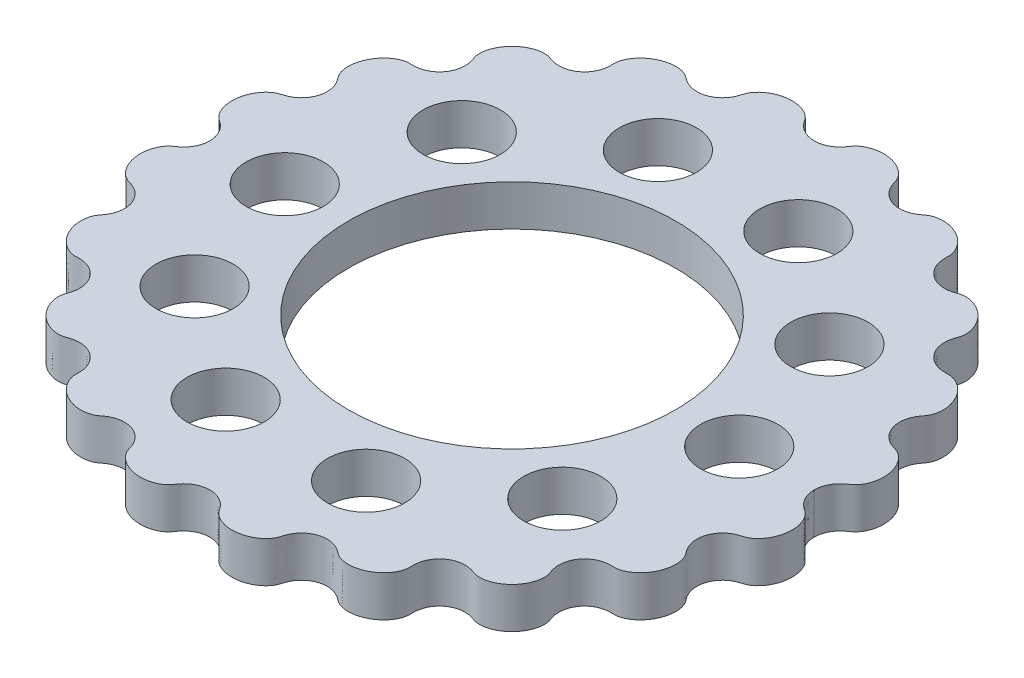
SolidWorks part; units mm, degrees
ref_plane "Front Plane" through (0, 0, 0) normal (0, 0, 1) x (1, 0, 0)
ref_plane "Top Plane" through (0, 0, 0) normal (0, 1, 0) x (1, 0, 0)
ref_plane "Right Plane" through (0, 0, 0) normal (1, 0, 0) x (0, 0, -1)
sketch "Sketch1" plane through (0, 0, 0) normal (0, 1, 0) x (1, 0, 0)
  line L0 (-115.1642, 0) -> (115.1642, 0) construction
  line L1 (0, 0) -> (50, 0)
  circle A0 centre (0, 0) radius 36
  circle A1 centre (50, 0) radius 8.5
  circle A2 centre (40.4508, -29.3893) radius 8.5
  circle A3 centre (15.4508, -47.5528) radius 8.5
  circle A4 centre (-15.4508, -47.5528) radius 8.5
  circle A5 centre (-40.4508, -29.3893) radius 8.5
  circle A6 centre (-50, 0) radius 8.5
  circle A7 centre (-40.4508, 29.3893) radius 8.5
  circle A8 centre (-15.4508, 47.5528) radius 8.5
  circle A9 centre (15.4508, 47.5528) radius 8.5
  circle A10 centre (40.4508, 29.3893) radius 8.5
  spline S0 degree 4 poles (65.4605, 29.5127) (65.4655, 29.1686) (65.4411, 28.6953) (65.3529, 28.0968) (65.1422, 27.3959) (64.9669, 26.9794) (64.7793, 26.6408) (64.5721, 26.3406) (64.3602, 26.0705) (64.1267, 25.7629) (63.886, 25.4071) (63.6576, 25.018) (63.4493, 24.5932) (63.2212, 24.0118) (63.0252, 23.2599) (62.9311, 22.3562) (63.0135, 21.3212) (63.2874, 20.3043) (63.7526, 19.3426) (64.4013, 18.4733) (65.1379, 17.8054) (65.8842, 17.3263) (66.5245, 17.0291) (66.9742, 16.8668) (67.3149, 16.7623) (67.5855, 16.6832) (67.8556, 16.6018) (68.139, 16.4927) (68.4292, 16.347) (68.7442, 16.1592) (69.1239, 15.8899) (69.5685, 15.5009) (70.0111, 15.0131) (70.4008, 14.4816) (70.6777, 14.0268) (70.8691, 13.6636) (70.9988, 13.3869) (71.0782, 13.2046) (71.1589, 13.0042) (71.23, 12.8148) (71.2726, 12.6939) (71.3209, 12.5457) (71.3774, 12.3645) (71.4665, 12.0546) (71.5573, 11.6609) (71.6461, 11.1378) (71.6973, 10.5855) (71.7141, 10.0755) (71.6934, 9.4422) (71.604, 8.684) (71.4252, 7.9197) (71.1461, 7.1625) (70.8392, 6.5565) (70.5425, 6.0894) (70.2317, 5.6994) (69.9193, 5.3829) (69.5974, 5.1276) (69.2839, 4.9185) (68.9179, 4.6631) (68.5115, 4.3444) (68.0178, 3.8822) (67.479, 3.228) (67.0049, 2.4212) (66.6487, 1.4477) (66.4722, 0.3979) (66.4959, -0.6726) (66.728, -1.7332) (67.1223, -2.6449) (67.6013, -3.3859) (68.0735, -3.9308) (68.4846, -4.3184) (68.8764, -4.6317) (69.2337, -4.8858) (69.5643, -5.1036) (69.8432, -5.3215) (70.1179, -5.5817) (70.4008, -5.9017) (70.7023, -6.3238) (71.0546, -6.9527) (71.3757, -7.7472) (71.6154, -8.6857) (71.7312, -9.759) (71.7014, -10.8232) (71.5361, -11.8601) (71.2442, -12.8535) (70.8335, -13.7883) (70.3588, -14.5657) (69.8607, -15.1916) (69.3853, -15.6662) (68.9647, -16.0122) (68.5481, -16.287) (68.1887, -16.4718) (67.8853, -16.5895) (67.6027, -16.679) (67.3177, -16.7605) (66.9147, -16.8851) (66.4027, -17.0799) (65.771, -17.3914) (65.047, -17.8802) (64.3539, -18.5333) (63.7378, -19.3727) (63.275, -20.3353) (63.0008, -21.3699) (62.9289, -22.4535) (63.0528, -23.4279) (63.2978, -24.2511) (63.587, -24.8932) (63.8609, -25.3718) (64.1452, -25.79) (64.4255, -26.1537) (64.7197, -26.5327) (64.9654, -26.9687) (65.1645, -27.4552) (65.3153, -27.9862) (65.4369, -28.6607) (65.4867, -29.4797) (65.4211, -30.426) (65.1959, -31.4778) (64.8335, -32.4836) (64.3459, -33.4278) (63.7436, -34.2955) (63.0364, -35.0719) (62.3194, -35.6676) (61.6326, -36.1029) (61.0186, -36.3975) (60.5014, -36.5851) (60.0027, -36.7056) (59.5828, -36.7546) (59.2387, -36.7552) (58.9195, -36.7455) (58.6002, -36.738) (58.1866, -36.7449) (57.6806, -36.7888) (57.0258, -36.9034) (56.2311, -37.1486) (55.3802, -37.5682) (54.5248, -38.2129) (53.7989, -39.0162) (53.2457, -39.9314) (52.8764, -40.9322) (52.7129, -41.9038) (52.7111, -42.801) (52.8153, -43.5274) (52.9414, -44.0332) (53.0556, -44.396) (53.1493, -44.6684) (53.2479, -44.939) (53.365, -45.2914) (53.4522, -45.7377) (53.492, -46.2577) (53.4686, -46.8459) (53.3634, -47.5564) (53.1367, -48.3745) (52.7684, -49.2465) (52.2349, -50.1437) (51.5838, -50.9705) (50.825, -51.7126) (49.9786, -52.3468) (49.0582, -52.8607) (48.2008, -53.1936) (47.4397, -53.384) (46.7836, -53.4712) (46.2434, -53.4905) (45.7356, -53.453) (45.3175, -53.3699) (44.9917, -53.2655) (44.6996, -53.161) (44.407, -53.0576) (44.0063, -52.933) (43.491, -52.8115) (42.8001, -52.7145) (41.9272, -52.71) (40.953, -52.8675) (39.9202, -53.2489) (38.9741, -53.8277) (38.1691, -54.5703) (37.5299, -55.4429) (37.1019, -56.344) (36.8793, -57.1248) (36.7803, -57.7595) (36.7454, -58.2289) (36.7381, -58.5957) (36.7456, -58.9543) (36.7588, -59.3048) (36.7453, -59.7001) (36.6779, -60.1352) (36.5493, -60.6146) (36.3491, -61.1297) (36.0405, -61.7408) (35.5897, -62.4233) (34.9769, -63.1346) (34.1812, -63.8335) (33.2956, -64.4242) (32.3354, -64.8968) (31.316, -65.2408) (30.2533, -65.4441) (29.3028, -65.4867) (28.4861, -65.415) (27.8172, -65.2736) (27.3586, -65.1269) (26.9828, -64.9645) (26.6415, -64.7795) (26.3825, -64.6044) (26.1435, -64.417) (25.8617, -64.202) (25.5735, -63.9954) (25.2136, -63.7661) (24.7736, -63.5314) (24.1733, -63.2738) (23.3906, -63.046) (22.4364, -62.9272) (21.3345, -63.0057) (20.2693, -63.297) (19.3028, -63.7777) (18.4651, -64.4155) (17.8212, -65.1237) (17.3489, -65.8446) (17.0492, -66.4737) (16.8796, -66.9362) (16.7731, -67.2787) (16.697, -67.538) (16.6206, -67.7971) (16.4999, -68.13) (16.3026, -68.5209) (16.0236, -68.9517) (15.6499, -69.4069) (15.1392, -69.9099) (14.4692, -70.4259) (13.6607, -70.8988) (12.7127, -71.2944) (11.702, -71.5708) (10.6433, -71.7174) (9.5744, -71.7223) (8.5152, -71.5812) (7.6197, -71.3301) (6.8918, -71.0218) (6.3681, -70.7238) (6.0257, -70.4887) (5.7564, -70.2722) (5.5526, -70.086) (5.3293, -69.8531) (5.1014, -69.5624) (4.8738, -69.215) (4.6046, -68.8398) (4.2946, -68.4584) (3.9347, -68.0813) (3.4174, -67.6285) (2.7042, -67.1529) (1.7921, -66.7433) (0.6851, -66.4941) (-0.4667, -66.4704) (-1.4606, -66.6552) (-2.2728, -66.9558) (-2.9107, -67.2974) (-3.3788, -67.6111) (-3.7983, -67.9554) (-4.1704, -68.3213) (-4.4603, -68.6577) (-4.6823, -68.9486) (-4.8581, -69.1976) (-4.9952, -69.3993) (-5.1396, -69.6076) (-5.3007, -69.8157) (-5.4839, -70.0179) (-5.6881, -70.2127) (-5.9591, -70.4393) (-6.3053, -70.6848) (-6.8327, -70.9933) (-7.5648, -71.3113) (-8.469, -71.5723) (-9.5418, -71.7212) (-10.6244, -71.7198) (-11.6959, -71.5725) (-12.7127, -71.2944) (-13.6607, -70.8988) (-14.4692, -70.4259) (-15.1392, -69.9099) (-15.6499, -69.4069) (-16.0236, -68.9517) (-16.3026, -68.5209) (-16.4999, -68.13) (-16.6206, -67.7971) (-16.697, -67.538) (-16.7731, -67.2787) (-16.8796, -66.9362) (-17.0492, -66.4737) (-17.3489, -65.8446) (-17.8212, -65.1237) (-18.4651, -64.4155) (-19.3028, -63.7777) (-20.2693, -63.297) (-21.3345, -63.0057) (-22.4364, -62.9272) (-23.3906, -63.046) (-24.1733, -63.2738) (-24.7736, -63.5314) (-25.2137, -63.7661) (-25.5735, -63.9954) (-25.8617, -64.202) (-26.0964, -64.3813) (-26.2831, -64.5262) (-26.4805, -64.6709) (-26.6936, -64.8076) (-26.9828, -64.9646) (-27.3587, -65.1269) (-27.8172, -65.2736) (-28.4861, -65.415) (-29.3028, -65.4868) (-30.2533, -65.4441) (-31.316, -65.2408) (-32.3354, -64.8968) (-33.2956, -64.4242) (-34.1812, -63.8335) (-34.9769, -63.1346) (-35.5897, -62.4233) (-36.0405, -61.7408) (-36.3491, -61.1297) (-36.5493, -60.6146) (-36.6779, -60.1352) (-36.7453, -59.7001) (-36.7588, -59.3048) (-36.7456, -58.9543) (-36.7381, -58.5957) (-36.7454, -58.2289) (-36.7803, -57.7595) (-36.8793, -57.1248) (-37.1019, -56.344) (-37.5299, -55.4429) (-38.1691, -54.5703) (-38.9741, -53.8277) (-39.9202, -53.2489) (-40.953, -52.8675) (-41.9272, -52.71) (-42.8001, -52.7145) (-43.491, -52.8115) (-44.0063, -52.933) (-44.407, -53.0576) (-44.6996, -53.161) (-44.9917, -53.2655) (-45.3175, -53.3699) (-45.7356, -53.453) (-46.2434, -53.4905) (-46.7836, -53.4712) (-47.4397, -53.384) (-48.2008, -53.1936) (-49.0582, -52.8607) (-49.9786, -52.3468) (-50.825, -51.7126) (-51.5838, -50.9705) (-52.2349, -50.1437) (-52.7684, -49.2465) (-53.1367, -48.3745) (-53.3634, -47.5564) (-53.4686, -46.8459) (-53.492, -46.2577) (-53.4522, -45.7377) (-53.365, -45.2914) (-53.2479, -44.939) (-53.1493, -44.6684) (-53.0556, -44.396) (-52.9697, -44.1229) (-52.8837, -43.8018) (-52.7883, -43.3387) (-52.7113, -42.7066) (-52.7129, -41.9038) (-52.8764, -40.9322) (-53.2457, -39.9314) (-53.7989, -39.0162) (-54.5248, -38.2129) (-55.3802, -37.5682) (-56.2311, -37.1486) (-57.0258, -36.9034) (-57.6806, -36.7888) (-58.1866, -36.7449) (-58.6002, -36.738) (-58.9195, -36.7455) (-59.2387, -36.7552) (-59.5828, -36.7546) (-60.0027, -36.7056) (-60.5014, -36.5851) (-61.0186, -36.3975) (-61.6326, -36.1029) (-62.3194, -35.6676) (-63.0364, -35.0719) (-63.7436, -34.2955) (-64.3459, -33.4278) (-64.8335, -32.4836) (-65.1959, -31.4778) (-65.4211, -30.426) (-65.4867, -29.4797) (-65.4369, -28.6607) (-65.3153, -27.9862) (-65.1645, -27.4552) (-64.9654, -26.9687) (-64.7197, -26.5327) (-64.4255, -26.1537) (-64.1452, -25.79) (-63.8609, -25.3718) (-63.587, -24.8932) (-63.2978, -24.2511) (-63.0528, -23.4279) (-62.9289, -22.4535) (-63.0008, -21.3699) (-63.275, -20.3353) (-63.7378, -19.3727) (-64.3539, -18.5333) (-65.047, -17.8802) (-65.771, -17.3914) (-66.4027, -17.0799) (-66.9147, -16.8851) (-67.3177, -16.7605) (-67.6027, -16.679) (-67.8853, -16.5895) (-68.1887, -16.4718) (-68.5481, -16.287) (-68.9647, -16.0122) (-69.3853, -15.6662) (-69.8607, -15.1916) (-70.3588, -14.5657) (-70.8335, -13.7883) (-71.2442, -12.8535) (-71.5361, -11.8601) (-71.7014, -10.8232) (-71.7312, -9.759) (-71.6154, -8.6857) (-71.3757, -7.7472) (-71.0546, -6.9527) (-70.7023, -6.3238) (-70.4008, -5.9017) (-70.1179, -5.5817) (-69.8432, -5.3215) (-69.5643, -5.1036) (-69.2337, -4.8858) (-68.8764, -4.6317) (-68.4846, -4.3184) (-68.0735, -3.9308) (-67.6013, -3.3859) (-67.1223, -2.6449) (-66.728, -1.7332) (-66.4959, -0.6726) (-66.4722, 0.3979) (-66.6487, 1.4477) (-67.0049, 2.4212) (-67.479, 3.228) (-68.0178, 3.8822) (-68.5115, 4.3445) (-68.9179, 4.6631) (-69.2839, 4.9185) (-69.5974, 5.1275) (-69.9193, 5.3829) (-70.2317, 5.6994) (-70.5425, 6.0895) (-70.8393, 6.5564) (-71.1461, 7.1627) (-71.4254, 7.9193) (-71.6038, 8.6846) (-71.6937, 9.4414) (-71.7137, 10.0768) (-71.6982, 10.5829) (-71.6528, 11.0541) (-71.5898, 11.476) (-71.5079, 11.8717) (-71.4425, 12.139) (-71.3774, 12.3645) (-71.3208, 12.546) (-71.2727, 12.6938) (-71.23, 12.8149) (-71.1589, 13.0042) (-71.0782, 13.2046) (-70.9988, 13.3869) (-70.8691, 13.6636) (-70.6777, 14.0268) (-70.4008, 14.4816) (-70.0111, 15.0131) (-69.5685, 15.5009) (-69.1239, 15.8899) (-68.7442, 16.1592) (-68.4292, 16.347) (-68.139, 16.4927) (-67.8556, 16.6018) (-67.5855, 16.6832) (-67.3149, 16.7623) (-66.9742, 16.8668) (-66.5245, 17.0291) (-65.8842, 17.3263) (-65.1379, 17.8054) (-64.4013, 18.4733) (-63.7491, 19.3473) (-63.28, 20.3205) (-63.0059, 21.3554) (-62.9309, 22.4063) (-63.0352, 23.3171) (-63.2396, 24.0678) (-63.4711, 24.642) (-63.6812, 25.0611) (-63.9101, 25.4449) (-64.1204, 25.7515) (-64.3116, 26.0062) (-64.4807, 26.2243) (-64.6214, 26.4108) (-64.7943, 26.6657) (-64.9775, 27.0024) (-65.1491, 27.4157) (-65.3551, 28.1105) (-65.4416, 28.7032) (-65.4654, 29.172) (-65.4605, 29.5127) knots 0 0 0 0 0 0.004123 0.005669 0.007215 0.008756 0.009527 0.010298 0.011583 0.012869 0.014155 0.015441 0.016987 0.018533 0.02163 0.024723 0.027815 0.030907 0.034179 0.03745 0.040732 0.042749 0.044767 0.045893 0.046456 0.04702 0.048146 0.049273 0.050089 0.050906 0.052538 0.054845 0.057151 0.058784 0.060416 0.061233 0.062049 0.062457 0.062865 0.063682 0.064216 0.064483 0.06475 0.065818 0.067955 0.069475 0.070996 0.072517 0.074037 0.077079 0.08012 0.0819 0.08368 0.085209 0.086738 0.087867 0.088995 0.090124 0.091252 0.093215 0.095179 0.098214 0.101374 0.104369 0.107533 0.1109 0.114125 0.117298 0.119365 0.121433 0.122746 0.124059 0.125372 0.126686 0.12749 0.128294 0.129902 0.131797 0.133692 0.136915 0.140139 0.143363 0.146587 0.149637 0.152687 0.155738 0.158788 0.160518 0.162248 0.163776 0.165304 0.166488 0.16708 0.167672 0.168855 0.170039 0.172134 0.174229 0.177278 0.18047 0.183483 0.186637 0.190007 0.193215 0.196415 0.198338 0.200262 0.201638 0.203015 0.204391 0.205768 0.207378 0.208989 0.210679 0.212369 0.215581 0.218794 0.222006 0.225218 0.228355 0.231492 0.234629 0.237765 0.239488 0.24121 0.242778 0.244347 0.245622 0.24626 0.246898 0.248174 0.24945 0.251214 0.252979 0.256128 0.259382 0.262517 0.265738 0.269027 0.272117 0.275225 0.277481 0.279736 0.280887 0.281463 0.282038 0.283189 0.28434 0.285906 0.287472 0.289426 0.29138 0.294497 0.297615 0.300733 0.30385 0.307074 0.310298 0.313371 0.316443 0.31806 0.319676 0.321293 0.322909 0.324149 0.324768 0.325388 0.326627 0.327867 0.329796 0.331725 0.334972 0.338289 0.341548 0.344836 0.34818 0.35133 0.354431 0.356724 0.35787 0.359017 0.360068 0.361118 0.362169 0.36322 0.3648 0.366381 0.368106 0.36983 0.372993 0.376156 0.379319 0.382483 0.385713 0.388944 0.392175 0.395406 0.397073 0.39874 0.400356 0.401164 0.401972 0.403388 0.404096 0.404804 0.40622 0.407635 0.409205 0.410774 0.414037 0.417372 0.420655 0.423928 0.427187 0.430227 0.4332 0.43534 0.437479 0.438558 0.439098 0.439638 0.440717 0.441796 0.443334 0.444872 0.446856 0.44884 0.451909 0.454977 0.458046 0.461115 0.464432 0.467749 0.470814 0.47388 0.475539 0.477198 0.478024 0.478851 0.479677 0.480504 0.481887 0.48327 0.484653 0.486036 0.487772 0.489508 0.492878 0.49627 0.499675 0.503014 0.506592 0.508301 0.51001 0.511672 0.513334 0.514795 0.516256 0.516987 0.517718 0.518448 0.519179 0.520024 0.520869 0.521714 0.522559 0.524254 0.525949 0.529024 0.532099 0.535492 0.538885 0.541954 0.545023 0.548091 0.55116 0.553144 0.555128 0.556666 0.558204 0.559283 0.560362 0.560902 0.561442 0.562521 0.56466 0.5668 0.569773 0.572812 0.576072 0.579345 0.582628 0.585963 0.589226 0.590795 0.592365 0.59378 0.595196 0.595904 0.596612 0.59732 0.598028 0.598836 0.599644 0.60126 0.602927 0.604594 0.607825 0.611056 0.614287 0.617517 0.620681 0.623844 0.627007 0.63017 0.631894 0.633619 0.635199 0.63678 0.637831 0.638882 0.639932 0.640983 0.64213 0.643276 0.645569 0.64867 0.65182 0.655164 0.658452 0.661711 0.665028 0.668275 0.670204 0.672133 0.673372 0.674612 0.675232 0.675851 0.677091 0.678707 0.680324 0.68194 0.683557 0.686629 0.689702 0.692926 0.69615 0.699267 0.702385 0.705503 0.70862 0.710574 0.712528 0.714094 0.71566 0.716811 0.717962 0.718537 0.719113 0.720264 0.721391 0.722519 0.724775 0.727883 0.730973 0.734262 0.737483 0.740618 0.743872 0.747021 0.748786 0.75055 0.751826 0.753102 0.75374 0.754378 0.755653 0.757222 0.75879 0.760512 0.762234 0.765371 0.768508 0.771645 0.774782 0.777994 0.781206 0.784419 0.787631 0.789321 0.791011 0.792622 0.794232 0.795609 0.796985 0.798362 0.799738 0.801662 0.803585 0.806785 0.809993 0.813363 0.816517 0.81953 0.822722 0.825771 0.827866 0.829961 0.831145 0.832328 0.83292 0.833512 0.834696 0.836224 0.837752 0.839482 0.841212 0.844262 0.847313 0.850363 0.853413 0.856637 0.859861 0.863084 0.866308 0.868203 0.870098 0.871706 0.87251 0.873314 0.874628 0.875941 0.877254 0.878567 0.880635 0.882702 0.885875 0.8891 0.892467 0.895631 0.898626 0.901786 0.904821 0.906785 0.908748 0.909876 0.911005 0.912133 0.913262 0.914791 0.91632 0.9181 0.91988 0.922921 0.925963 0.927483 0.929004 0.930525 0.932045 0.933114 0.934182 0.93525 0.935517 0.935784 0.936318 0.937135 0.937543 0.937951 0.938767 0.939584 0.941216 0.942849 0.945155 0.947462 0.949094 0.949911 0.950727 0.951854 0.95298 0.953544 0.954107 0.955233 0.957251 0.959268 0.96255 0.965821 0.969093 0.972255 0.975418 0.978575 0.981646 0.98318 0.984714 0.985986 0.987258 0.98853 0.989166 0.989802 0.990566 0.991329 0.992855 0.994386 0.995917 1 1 1 1 1 construction
  spline S1 degree 4 poles (66.5, 0) (66.5, -0.3064) (66.5419, -0.882) (66.7179, -1.7097) (67.1223, -2.6449) (67.6013, -3.3859) (68.0735, -3.9308) (68.4846, -4.3184) (68.8764, -4.6317) (69.2337, -4.8858) (69.5643, -5.1036) (69.8432, -5.3215) (70.1179, -5.5817) (70.4008, -5.9017) (70.7023, -6.3238) (71.0546, -6.9527) (71.3757, -7.7472) (71.6154, -8.6857) (71.7312, -9.759) (71.7014, -10.8232) (71.5361, -11.8601) (71.2442, -12.8535) (70.8335, -13.7883) (70.3588, -14.5657) (69.8607, -15.1916) (69.3853, -15.6662) (68.9647, -16.0122) (68.5481, -16.287) (68.1887, -16.4718) (67.8853, -16.5895) (67.6027, -16.679) (67.3177, -16.7605) (66.9147, -16.8851) (66.4027, -17.0799) (65.771, -17.3914) (65.047, -17.8802) (64.3539, -18.5333) (63.7378, -19.3727) (63.275, -20.3353) (63.0008, -21.3699) (62.9289, -22.4535) (63.0528, -23.4279) (63.2978, -24.2511) (63.587, -24.8932) (63.8609, -25.3718) (64.1452, -25.79) (64.4255, -26.1537) (64.7197, -26.5327) (64.9654, -26.9687) (65.1645, -27.4552) (65.3153, -27.9862) (65.4369, -28.6607) (65.4867, -29.4797) (65.4211, -30.426) (65.1959, -31.4778) (64.8335, -32.4836) (64.3459, -33.4278) (63.7436, -34.2955) (63.0364, -35.0719) (62.3194, -35.6676) (61.6326, -36.1029) (61.0186, -36.3975) (60.5014, -36.5851) (60.0027, -36.7056) (59.5828, -36.7546) (59.2387, -36.7552) (58.9195, -36.7455) (58.6002, -36.738) (58.1866, -36.7449) (57.6806, -36.7888) (57.0258, -36.9034) (56.2311, -37.1486) (55.3802, -37.5682) (54.5248, -38.2129) (53.7989, -39.0162) (53.2457, -39.9314) (52.8764, -40.9322) (52.7129, -41.9038) (52.7111, -42.801) (52.8153, -43.5274) (52.9414, -44.0332) (53.0556, -44.396) (53.1493, -44.6684) (53.2479, -44.939) (53.365, -45.2914) (53.4522, -45.7377) (53.492, -46.2577) (53.4686, -46.8459) (53.3634, -47.5564) (53.1367, -48.3745) (52.7684, -49.2465) (52.2349, -50.1437) (51.5838, -50.9705) (50.825, -51.7126) (49.9786, -52.3468) (49.0582, -52.8607) (48.2008, -53.1936) (47.4397, -53.384) (46.7836, -53.4712) (46.2434, -53.4905) (45.7356, -53.453) (45.3175, -53.3699) (44.9917, -53.2655) (44.6996, -53.161) (44.407, -53.0576) (44.0063, -52.933) (43.491, -52.8115) (42.8001, -52.7145) (41.9272, -52.71) (40.953, -52.8675) (39.9202, -53.2489) (38.9741, -53.8277) (38.1691, -54.5703) (37.5299, -55.4429) (37.1019, -56.344) (36.8793, -57.1248) (36.7803, -57.7595) (36.7454, -58.2289) (36.7381, -58.5957) (36.7456, -58.9543) (36.7588, -59.3048) (36.7453, -59.7001) (36.6779, -60.1352) (36.5493, -60.6146) (36.3491, -61.1297) (36.0405, -61.7408) (35.5897, -62.4233) (34.9769, -63.1346) (34.1812, -63.8335) (33.2956, -64.4242) (32.3354, -64.8968) (31.316, -65.2408) (30.2533, -65.4441) (29.3028, -65.4867) (28.4861, -65.415) (27.8172, -65.2736) (27.3586, -65.1269) (26.9828, -64.9645) (26.6415, -64.7795) (26.3825, -64.6044) (26.1435, -64.417) (25.8617, -64.202) (25.5735, -63.9954) (25.2136, -63.7661) (24.7736, -63.5314) (24.1733, -63.2738) (23.3906, -63.046) (22.4364, -62.9272) (21.3345, -63.0057) (20.2693, -63.297) (19.3028, -63.7777) (18.4651, -64.4155) (17.8212, -65.1237) (17.3489, -65.8446) (17.0492, -66.4737) (16.8796, -66.9362) (16.7731, -67.2787) (16.697, -67.538) (16.6206, -67.7971) (16.4999, -68.13) (16.3026, -68.5209) (16.0236, -68.9517) (15.6499, -69.4069) (15.1392, -69.9099) (14.4692, -70.4259) (13.6607, -70.8988) (12.7127, -71.2944) (11.702, -71.5708) (10.6433, -71.7174) (9.5744, -71.7223) (8.5152, -71.5812) (7.6197, -71.3301) (6.8918, -71.0218) (6.3681, -70.7238) (6.0257, -70.4887) (5.7564, -70.2722) (5.5526, -70.086) (5.3293, -69.8531) (5.1014, -69.5624) (4.8738, -69.215) (4.6046, -68.8398) (4.2946, -68.4584) (3.9347, -68.0813) (3.4174, -67.6285) (2.7042, -67.1529) (1.7921, -66.7433) (0.6851, -66.4941) (-0.4667, -66.4704) (-1.4606, -66.6552) (-2.2728, -66.9558) (-2.9107, -67.2974) (-3.3788, -67.6111) (-3.7983, -67.9554) (-4.1704, -68.3213) (-4.4603, -68.6577) (-4.6823, -68.9486) (-4.8581, -69.1976) (-4.9952, -69.3993) (-5.1396, -69.6076) (-5.3007, -69.8157) (-5.4839, -70.0179) (-5.6881, -70.2127) (-5.9591, -70.4393) (-6.3053, -70.6848) (-6.8327, -70.9933) (-7.5648, -71.3113) (-8.469, -71.5723) (-9.5418, -71.7212) (-10.6244, -71.7198) (-11.6959, -71.5725) (-12.7127, -71.2944) (-13.6607, -70.8988) (-14.4692, -70.4259) (-15.1392, -69.9099) (-15.6499, -69.4069) (-16.0236, -68.9517) (-16.3026, -68.5209) (-16.4999, -68.13) (-16.6206, -67.7971) (-16.697, -67.538) (-16.7731, -67.2787) (-16.8796, -66.9362) (-17.0492, -66.4737) (-17.3489, -65.8446) (-17.8212, -65.1237) (-18.4651, -64.4155) (-19.3028, -63.7777) (-20.2693, -63.297) (-21.3345, -63.0057) (-22.4364, -62.9272) (-23.3906, -63.046) (-24.1733, -63.2738) (-24.7736, -63.5314) (-25.2137, -63.7661) (-25.5735, -63.9954) (-25.8617, -64.202) (-26.0964, -64.3813) (-26.2831, -64.5262) (-26.4805, -64.6709) (-26.6936, -64.8076) (-26.9828, -64.9646) (-27.3587, -65.1269) (-27.8172, -65.2736) (-28.4861, -65.415) (-29.3028, -65.4868) (-30.2533, -65.4441) (-31.316, -65.2408) (-32.3354, -64.8968) (-33.2956, -64.4242) (-34.1812, -63.8335) (-34.9769, -63.1346) (-35.5897, -62.4233) (-36.0405, -61.7408) (-36.3491, -61.1297) (-36.5493, -60.6146) (-36.6779, -60.1352) (-36.7453, -59.7001) (-36.7588, -59.3048) (-36.7456, -58.9543) (-36.7381, -58.5957) (-36.7454, -58.2289) (-36.7803, -57.7595) (-36.8793, -57.1248) (-37.1019, -56.344) (-37.5299, -55.4429) (-38.1691, -54.5703) (-38.9741, -53.8277) (-39.9202, -53.2489) (-40.953, -52.8675) (-41.9272, -52.71) (-42.8001, -52.7145) (-43.491, -52.8115) (-44.0063, -52.933) (-44.407, -53.0576) (-44.6996, -53.161) (-44.9917, -53.2655) (-45.3175, -53.3699) (-45.7356, -53.453) (-46.2434, -53.4905) (-46.7836, -53.4712) (-47.4397, -53.384) (-48.2008, -53.1936) (-49.0582, -52.8607) (-49.9786, -52.3468) (-50.825, -51.7126) (-51.5838, -50.9705) (-52.2349, -50.1437) (-52.7684, -49.2465) (-53.1367, -48.3745) (-53.3634, -47.5564) (-53.4686, -46.8459) (-53.492, -46.2577) (-53.4522, -45.7377) (-53.365, -45.2914) (-53.2479, -44.939) (-53.1493, -44.6684) (-53.0556, -44.396) (-52.9697, -44.1229) (-52.8837, -43.8018) (-52.7883, -43.3387) (-52.7113, -42.7066) (-52.7129, -41.9038) (-52.8764, -40.9322) (-53.2457, -39.9314) (-53.7989, -39.0162) (-54.5248, -38.2129) (-55.3802, -37.5682) (-56.2311, -37.1486) (-57.0258, -36.9034) (-57.6806, -36.7888) (-58.1866, -36.7449) (-58.6002, -36.738) (-58.9195, -36.7455) (-59.2387, -36.7552) (-59.5828, -36.7546) (-60.0027, -36.7056) (-60.5014, -36.5851) (-61.0186, -36.3975) (-61.6326, -36.1029) (-62.3194, -35.6676) (-63.0364, -35.0719) (-63.7436, -34.2955) (-64.3459, -33.4278) (-64.8335, -32.4836) (-65.1959, -31.4778) (-65.4211, -30.426) (-65.4867, -29.4797) (-65.4369, -28.6607) (-65.3153, -27.9862) (-65.1645, -27.4552) (-64.9654, -26.9687) (-64.7197, -26.5327) (-64.4255, -26.1537) (-64.1452, -25.79) (-63.8609, -25.3718) (-63.587, -24.8932) (-63.2978, -24.2511) (-63.0528, -23.4279) (-62.9289, -22.4535) (-63.0008, -21.3699) (-63.275, -20.3353) (-63.7378, -19.3727) (-64.3539, -18.5333) (-65.047, -17.8802) (-65.771, -17.3914) (-66.4027, -17.0799) (-66.9147, -16.8851) (-67.3177, -16.7605) (-67.6027, -16.679) (-67.8853, -16.5895) (-68.1887, -16.4718) (-68.5481, -16.287) (-68.9647, -16.0122) (-69.3853, -15.6662) (-69.8607, -15.1916) (-70.3588, -14.5657) (-70.8335, -13.7883) (-71.2442, -12.8535) (-71.5361, -11.8601) (-71.7014, -10.8232) (-71.7312, -9.759) (-71.6154, -8.6857) (-71.3757, -7.7472) (-71.0546, -6.9527) (-70.7023, -6.3238) (-70.4008, -5.9017) (-70.1179, -5.5817) (-69.8432, -5.3215) (-69.5643, -5.1036) (-69.2337, -4.8858) (-68.8764, -4.6317) (-68.4846, -4.3184) (-68.0735, -3.9308) (-67.6013, -3.3859) (-67.1223, -2.6449) (-66.7179, -1.7097) (-66.5419, -0.882) (-66.5, -0.3064) (-66.5, 0) knots 0.107228 0.107228 0.107228 0.107228 0.107228 0.1109 0.114125 0.117298 0.119365 0.121433 0.122746 0.124059 0.125372 0.126686 0.12749 0.128294 0.129902 0.131797 0.133692 0.136915 0.140139 0.143363 0.146587 0.149637 0.152687 0.155738 0.158788 0.160518 0.162248 0.163776 0.165304 0.166488 0.16708 0.167672 0.168855 0.170039 0.172134 0.174229 0.177278 0.18047 0.183483 0.186637 0.190007 0.193215 0.196415 0.198338 0.200262 0.201638 0.203015 0.204391 0.205768 0.207378 0.208989 0.210679 0.212369 0.215581 0.218794 0.222006 0.225218 0.228355 0.231492 0.234629 0.237765 0.239488 0.24121 0.242778 0.244347 0.245622 0.24626 0.246898 0.248174 0.24945 0.251214 0.252979 0.256128 0.259382 0.262517 0.265738 0.269027 0.272117 0.275225 0.277481 0.279736 0.280887 0.281463 0.282038 0.283189 0.28434 0.285906 0.287472 0.289426 0.29138 0.294497 0.297615 0.300733 0.30385 0.307074 0.310298 0.313371 0.316443 0.31806 0.319676 0.321293 0.322909 0.324149 0.324768 0.325388 0.326627 0.327867 0.329796 0.331725 0.334972 0.338289 0.341548 0.344836 0.34818 0.35133 0.354431 0.356724 0.35787 0.359017 0.360068 0.361118 0.362169 0.36322 0.3648 0.366381 0.368106 0.36983 0.372993 0.376156 0.379319 0.382483 0.385713 0.388944 0.392175 0.395406 0.397073 0.39874 0.400356 0.401164 0.401972 0.403388 0.404096 0.404804 0.40622 0.407635 0.409205 0.410774 0.414037 0.417372 0.420655 0.423928 0.427187 0.430227 0.4332 0.43534 0.437479 0.438558 0.439098 0.439638 0.440717 0.441796 0.443334 0.444872 0.446856 0.44884 0.451909 0.454977 0.458046 0.461115 0.464432 0.467749 0.470814 0.47388 0.475539 0.477198 0.478024 0.478851 0.479677 0.480504 0.481887 0.48327 0.484653 0.486036 0.487772 0.489508 0.492878 0.49627 0.499675 0.503014 0.506592 0.508301 0.51001 0.511672 0.513334 0.514795 0.516256 0.516987 0.517718 0.518448 0.519179 0.520024 0.520869 0.521714 0.522559 0.524254 0.525949 0.529024 0.532099 0.535492 0.538885 0.541954 0.545023 0.548091 0.55116 0.553144 0.555128 0.556666 0.558204 0.559283 0.560362 0.560902 0.561442 0.562521 0.56466 0.5668 0.569773 0.572812 0.576072 0.579345 0.582628 0.585963 0.589226 0.590795 0.592365 0.59378 0.595196 0.595904 0.596612 0.59732 0.598028 0.598836 0.599644 0.60126 0.602927 0.604594 0.607825 0.611056 0.614287 0.617517 0.620681 0.623844 0.627007 0.63017 0.631894 0.633619 0.635199 0.63678 0.637831 0.638882 0.639932 0.640983 0.64213 0.643276 0.645569 0.64867 0.65182 0.655164 0.658452 0.661711 0.665028 0.668275 0.670204 0.672133 0.673372 0.674612 0.675232 0.675851 0.677091 0.678707 0.680324 0.68194 0.683557 0.686629 0.689702 0.692926 0.69615 0.699267 0.702385 0.705503 0.70862 0.710574 0.712528 0.714094 0.71566 0.716811 0.717962 0.718537 0.719113 0.720264 0.721391 0.722519 0.724775 0.727883 0.730973 0.734262 0.737483 0.740618 0.743872 0.747021 0.748786 0.75055 0.751826 0.753102 0.75374 0.754378 0.755653 0.757222 0.75879 0.760512 0.762234 0.765371 0.768508 0.771645 0.774782 0.777994 0.781206 0.784419 0.787631 0.789321 0.791011 0.792622 0.794232 0.795609 0.796985 0.798362 0.799738 0.801662 0.803585 0.806785 0.809993 0.813363 0.816517 0.81953 0.822722 0.825771 0.827866 0.829961 0.831145 0.832328 0.83292 0.833512 0.834696 0.836224 0.837752 0.839482 0.841212 0.844262 0.847313 0.850363 0.853413 0.856637 0.859861 0.863084 0.866308 0.868203 0.870098 0.871706 0.87251 0.873314 0.874628 0.875941 0.877254 0.878567 0.880635 0.882702 0.885875 0.8891 0.892772 0.892772 0.892772 0.892772 0.892772
  spline S2 degree 4 poles (66.5, 0) (66.5, 0.3064) (66.5419, 0.882) (66.7179, 1.7097) (67.1223, 2.6449) (67.6013, 3.3859) (68.0735, 3.9308) (68.4846, 4.3184) (68.8764, 4.6317) (69.2337, 4.8858) (69.5643, 5.1036) (69.8432, 5.3215) (70.1179, 5.5817) (70.4008, 5.9017) (70.7023, 6.3238) (71.0546, 6.9527) (71.3757, 7.7472) (71.6154, 8.6857) (71.7312, 9.759) (71.7014, 10.8232) (71.5361, 11.8601) (71.2442, 12.8535) (70.8335, 13.7883) (70.3588, 14.5657) (69.8607, 15.1916) (69.3853, 15.6662) (68.9647, 16.0122) (68.5481, 16.287) (68.1887, 16.4718) (67.8853, 16.5895) (67.6027, 16.679) (67.3177, 16.7605) (66.9147, 16.8851) (66.4027, 17.0799) (65.771, 17.3914) (65.047, 17.8802) (64.3539, 18.5333) (63.7378, 19.3727) (63.275, 20.3353) (63.0008, 21.3699) (62.9289, 22.4535) (63.0528, 23.4279) (63.2978, 24.2511) (63.587, 24.8932) (63.8609, 25.3718) (64.1452, 25.79) (64.4255, 26.1537) (64.7197, 26.5327) (64.9654, 26.9687) (65.1645, 27.4552) (65.3153, 27.9862) (65.4369, 28.6607) (65.4867, 29.4797) (65.4211, 30.426) (65.1959, 31.4778) (64.8335, 32.4836) (64.3459, 33.4278) (63.7436, 34.2955) (63.0364, 35.0719) (62.3194, 35.6676) (61.6326, 36.1029) (61.0186, 36.3975) (60.5014, 36.5851) (60.0027, 36.7056) (59.5828, 36.7546) (59.2387, 36.7552) (58.9195, 36.7455) (58.6002, 36.738) (58.1866, 36.7449) (57.6806, 36.7888) (57.0258, 36.9034) (56.2311, 37.1486) (55.3802, 37.5682) (54.5248, 38.2129) (53.7989, 39.0162) (53.2457, 39.9314) (52.8764, 40.9322) (52.7129, 41.9038) (52.7111, 42.801) (52.8153, 43.5274) (52.9414, 44.0332) (53.0556, 44.396) (53.1493, 44.6684) (53.2479, 44.939) (53.365, 45.2914) (53.4522, 45.7377) (53.492, 46.2577) (53.4686, 46.8459) (53.3634, 47.5564) (53.1367, 48.3745) (52.7684, 49.2465) (52.2349, 50.1437) (51.5838, 50.9705) (50.825, 51.7126) (49.9786, 52.3469) (49.0582, 52.8607) (48.2008, 53.1936) (47.4397, 53.384) (46.7836, 53.4712) (46.2434, 53.4905) (45.7356, 53.453) (45.3175, 53.3699) (44.9917, 53.2655) (44.6996, 53.161) (44.407, 53.0576) (44.0063, 52.933) (43.491, 52.8115) (42.8001, 52.7145) (41.9272, 52.71) (40.953, 52.8675) (39.9202, 53.2489) (38.9741, 53.8277) (38.1691, 54.5703) (37.5299, 55.4429) (37.1019, 56.344) (36.8793, 57.1248) (36.7803, 57.7595) (36.7454, 58.2289) (36.7381, 58.5957) (36.7456, 58.9543) (36.7588, 59.3048) (36.7453, 59.7001) (36.6779, 60.1352) (36.5493, 60.6146) (36.3491, 61.1297) (36.0405, 61.7408) (35.5897, 62.4233) (34.9769, 63.1346) (34.1812, 63.8335) (33.2956, 64.4242) (32.3354, 64.8968) (31.316, 65.2408) (30.2533, 65.4441) (29.3028, 65.4867) (28.4861, 65.415) (27.8172, 65.2736) (27.3586, 65.1269) (26.9828, 64.9645) (26.6415, 64.7795) (26.3825, 64.6044) (26.1435, 64.417) (25.8617, 64.202) (25.5735, 63.9954) (25.2136, 63.7661) (24.7736, 63.5314) (24.1733, 63.2738) (23.3906, 63.046) (22.4364, 62.9272) (21.3345, 63.0057) (20.2693, 63.297) (19.3028, 63.7777) (18.4651, 64.4155) (17.8212, 65.1237) (17.3489, 65.8446) (17.0492, 66.4737) (16.8796, 66.9362) (16.7731, 67.2787) (16.697, 67.538) (16.6206, 67.7971) (16.4999, 68.13) (16.3026, 68.5209) (16.0236, 68.9517) (15.6499, 69.4069) (15.1392, 69.9099) (14.4692, 70.4259) (13.6607, 70.8988) (12.7127, 71.2944) (11.702, 71.5708) (10.6433, 71.7174) (9.5744, 71.7223) (8.5152, 71.5812) (7.6197, 71.3301) (6.8918, 71.0218) (6.3681, 70.7238) (6.0257, 70.4887) (5.7564, 70.2722) (5.5526, 70.086) (5.3293, 69.8531) (5.1014, 69.5624) (4.8738, 69.215) (4.6046, 68.8398) (4.2946, 68.4584) (3.9347, 68.0813) (3.4174, 67.6285) (2.7042, 67.1529) (1.7921, 66.7433) (0.6851, 66.4941) (-0.4667, 66.4704) (-1.4606, 66.6552) (-2.2728, 66.9558) (-2.9107, 67.2974) (-3.3788, 67.6111) (-3.7983, 67.9554) (-4.1704, 68.3213) (-4.4603, 68.6577) (-4.6823, 68.9486) (-4.8581, 69.1976) (-4.9952, 69.3993) (-5.1396, 69.6076) (-5.3007, 69.8157) (-5.4839, 70.0179) (-5.6881, 70.2127) (-5.9591, 70.4393) (-6.3053, 70.6848) (-6.8327, 70.9933) (-7.5648, 71.3113) (-8.469, 71.5723) (-9.5418, 71.7212) (-10.6244, 71.7198) (-11.6959, 71.5725) (-12.7127, 71.2944) (-13.6607, 70.8988) (-14.4692, 70.4259) (-15.1392, 69.9099) (-15.6499, 69.4069) (-16.0236, 68.9517) (-16.3026, 68.5209) (-16.4999, 68.13) (-16.6206, 67.7971) (-16.697, 67.538) (-16.7731, 67.2787) (-16.8796, 66.9362) (-17.0492, 66.4737) (-17.3489, 65.8446) (-17.8212, 65.1237) (-18.4651, 64.4155) (-19.3028, 63.7777) (-20.2693, 63.297) (-21.3345, 63.0057) (-22.4364, 62.9272) (-23.3906, 63.046) (-24.1733, 63.2738) (-24.7736, 63.5314) (-25.2137, 63.7661) (-25.5735, 63.9954) (-25.8617, 64.202) (-26.0964, 64.3813) (-26.2831, 64.5262) (-26.4805, 64.6709) (-26.6936, 64.8076) (-26.9828, 64.9646) (-27.3587, 65.1269) (-27.8172, 65.2736) (-28.4861, 65.415) (-29.3028, 65.4868) (-30.2533, 65.4441) (-31.316, 65.2408) (-32.3354, 64.8968) (-33.2956, 64.4242) (-34.1812, 63.8335) (-34.9769, 63.1346) (-35.5897, 62.4233) (-36.0405, 61.7408) (-36.3491, 61.1297) (-36.5493, 60.6146) (-36.6779, 60.1352) (-36.7453, 59.7001) (-36.7588, 59.3048) (-36.7456, 58.9543) (-36.7381, 58.5957) (-36.7454, 58.2289) (-36.7803, 57.7595) (-36.8793, 57.1248) (-37.1019, 56.344) (-37.5299, 55.4429) (-38.1691, 54.5703) (-38.9741, 53.8277) (-39.9202, 53.2489) (-40.953, 52.8675) (-41.9272, 52.71) (-42.8001, 52.7145) (-43.491, 52.8115) (-44.0063, 52.933) (-44.407, 53.0576) (-44.6996, 53.161) (-44.9917, 53.2655) (-45.3175, 53.3699) (-45.7356, 53.453) (-46.2434, 53.4905) (-46.7836, 53.4712) (-47.4397, 53.384) (-48.2008, 53.1936) (-49.0582, 52.8607) (-49.9786, 52.3469) (-50.825, 51.7126) (-51.5838, 50.9705) (-52.2349, 50.1437) (-52.7684, 49.2465) (-53.1367, 48.3745) (-53.3634, 47.5564) (-53.4686, 46.8459) (-53.492, 46.2577) (-53.4522, 45.7377) (-53.365, 45.2914) (-53.2479, 44.939) (-53.1493, 44.6684) (-53.0556, 44.396) (-52.9697, 44.1229) (-52.8837, 43.8018) (-52.7883, 43.3387) (-52.7113, 42.7066) (-52.7129, 41.9038) (-52.8764, 40.9322) (-53.2457, 39.9314) (-53.7989, 39.0162) (-54.5248, 38.2129) (-55.3802, 37.5682) (-56.2311, 37.1486) (-57.0258, 36.9034) (-57.6806, 36.7888) (-58.1866, 36.7449) (-58.6002, 36.738) (-58.9195, 36.7455) (-59.2387, 36.7552) (-59.5828, 36.7546) (-60.0027, 36.7056) (-60.5014, 36.5851) (-61.0186, 36.3975) (-61.6326, 36.1029) (-62.3194, 35.6676) (-63.0364, 35.0719) (-63.7436, 34.2955) (-64.3459, 33.4278) (-64.8335, 32.4836) (-65.1959, 31.4778) (-65.4211, 30.426) (-65.4867, 29.4797) (-65.4369, 28.6607) (-65.3153, 27.9862) (-65.1645, 27.4552) (-64.9654, 26.9687) (-64.7197, 26.5327) (-64.4255, 26.1537) (-64.1452, 25.79) (-63.8609, 25.3718) (-63.587, 24.8932) (-63.2978, 24.2511) (-63.0528, 23.4279) (-62.9289, 22.4535) (-63.0008, 21.3699) (-63.275, 20.3353) (-63.7378, 19.3727) (-64.3539, 18.5333) (-65.047, 17.8802) (-65.771, 17.3914) (-66.4027, 17.0799) (-66.9147, 16.8851) (-67.3177, 16.7605) (-67.6027, 16.679) (-67.8853, 16.5895) (-68.1887, 16.4718) (-68.5481, 16.287) (-68.9647, 16.0122) (-69.3853, 15.6662) (-69.8607, 15.1916) (-70.3588, 14.5657) (-70.8335, 13.7883) (-71.2442, 12.8535) (-71.5361, 11.8601) (-71.7014, 10.8232) (-71.7312, 9.759) (-71.6154, 8.6857) (-71.3757, 7.7472) (-71.0546, 6.9527) (-70.7023, 6.3238) (-70.4008, 5.9017) (-70.1179, 5.5817) (-69.8432, 5.3215) (-69.5643, 5.1036) (-69.2337, 4.8858) (-68.8764, 4.6317) (-68.4846, 4.3184) (-68.0735, 3.9308) (-67.6013, 3.3859) (-67.1223, 2.6449) (-66.7179, 1.7097) (-66.5419, 0.882) (-66.5, 0.3064) (-66.5, 0) knots 0.107228 0.107228 0.107228 0.107228 0.107228 0.1109 0.114125 0.117298 0.119365 0.121433 0.122746 0.124059 0.125372 0.126686 0.12749 0.128294 0.129902 0.131797 0.133692 0.136915 0.140139 0.143363 0.146587 0.149637 0.152687 0.155738 0.158788 0.160518 0.162248 0.163776 0.165304 0.166488 0.16708 0.167672 0.168855 0.170039 0.172134 0.174229 0.177278 0.18047 0.183483 0.186637 0.190007 0.193215 0.196415 0.198338 0.200262 0.201638 0.203015 0.204391 0.205768 0.207378 0.208989 0.210679 0.212369 0.215581 0.218794 0.222006 0.225218 0.228355 0.231492 0.234629 0.237765 0.239488 0.24121 0.242778 0.244347 0.245622 0.24626 0.246898 0.248174 0.24945 0.251214 0.252979 0.256128 0.259382 0.262517 0.265738 0.269027 0.272117 0.275225 0.277481 0.279736 0.280887 0.281463 0.282038 0.283189 0.28434 0.285906 0.287472 0.289426 0.29138 0.294497 0.297615 0.300733 0.30385 0.307074 0.310298 0.313371 0.316443 0.31806 0.319676 0.321293 0.322909 0.324149 0.324768 0.325388 0.326627 0.327867 0.329796 0.331725 0.334972 0.338289 0.341548 0.344836 0.34818 0.35133 0.354431 0.356724 0.35787 0.359017 0.360068 0.361118 0.362169 0.36322 0.3648 0.366381 0.368106 0.36983 0.372993 0.376156 0.379319 0.382483 0.385713 0.388944 0.392175 0.395406 0.397073 0.39874 0.400356 0.401164 0.401972 0.403388 0.404096 0.404804 0.40622 0.407635 0.409205 0.410774 0.414037 0.417372 0.420655 0.423928 0.427187 0.430227 0.4332 0.43534 0.437479 0.438558 0.439098 0.439638 0.440717 0.441796 0.443334 0.444872 0.446856 0.44884 0.451909 0.454977 0.458046 0.461115 0.464432 0.467749 0.470814 0.47388 0.475539 0.477198 0.478024 0.478851 0.479677 0.480504 0.481887 0.48327 0.484653 0.486036 0.487772 0.489508 0.492878 0.49627 0.499675 0.503014 0.506592 0.508301 0.51001 0.511672 0.513334 0.514795 0.516256 0.516987 0.517718 0.518448 0.519179 0.520024 0.520869 0.521714 0.522559 0.524254 0.525949 0.529024 0.532099 0.535492 0.538885 0.541954 0.545023 0.548091 0.55116 0.553144 0.555128 0.556666 0.558204 0.559283 0.560362 0.560902 0.561442 0.562521 0.56466 0.5668 0.569773 0.572812 0.576072 0.579345 0.582628 0.585963 0.589226 0.590795 0.592365 0.59378 0.595196 0.595904 0.596612 0.59732 0.598028 0.598836 0.599644 0.60126 0.602927 0.604594 0.607825 0.611056 0.614287 0.617517 0.620681 0.623844 0.627007 0.63017 0.631894 0.633619 0.635199 0.63678 0.637831 0.638882 0.639932 0.640983 0.64213 0.643276 0.645569 0.64867 0.65182 0.655164 0.658452 0.661711 0.665028 0.668275 0.670204 0.672133 0.673372 0.674612 0.675232 0.675851 0.677091 0.678707 0.680324 0.68194 0.683557 0.686629 0.689702 0.692926 0.69615 0.699267 0.702385 0.705503 0.70862 0.710574 0.712528 0.714094 0.71566 0.716811 0.717962 0.718537 0.719113 0.720264 0.721391 0.722519 0.724775 0.727883 0.730973 0.734262 0.737483 0.740618 0.743872 0.747021 0.748786 0.75055 0.751826 0.753102 0.75374 0.754378 0.755653 0.757222 0.75879 0.760512 0.762234 0.765371 0.768508 0.771645 0.774782 0.777994 0.781206 0.784419 0.787631 0.789321 0.791011 0.792622 0.794232 0.795609 0.796985 0.798362 0.799738 0.801662 0.803585 0.806785 0.809993 0.813363 0.816517 0.81953 0.822722 0.825771 0.827866 0.829961 0.831145 0.832328 0.83292 0.833512 0.834696 0.836224 0.837752 0.839482 0.841212 0.844262 0.847313 0.850363 0.853413 0.856637 0.859861 0.863084 0.866308 0.868203 0.870098 0.871706 0.87251 0.873314 0.874628 0.875941 0.877254 0.878567 0.880635 0.882702 0.885875 0.8891 0.892772 0.892772 0.892772 0.892772 0.892772
  point P8 (0, 0)
  point P33 (0, 0)
  dimension "D1" = 10
extrude "Boss-Extrude1" add sketch "Sketch1" along normal blind 9
